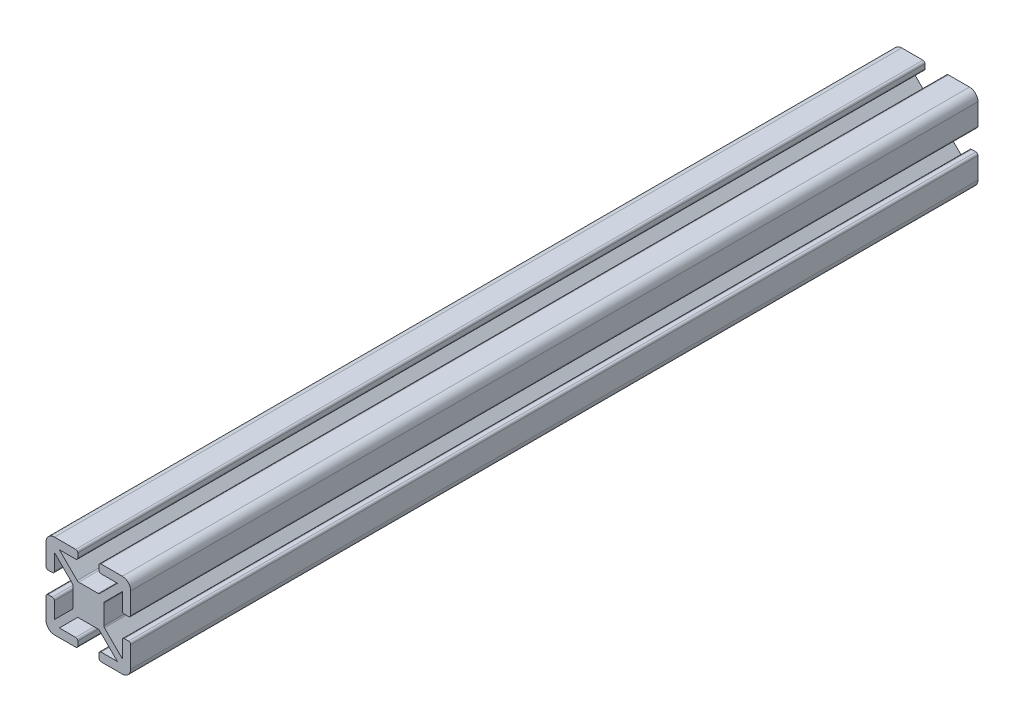
SolidWorks part; units mm, degrees
ref_plane "Ebene vorne" through (0, 0, 0) normal (0, 0, 1) x (1, 0, 0)
ref_plane "Ebene oben" through (0, 0, 0) normal (0, 1, 0) x (1, 0, 0)
ref_plane "Ebene rechts" through (0, 0, 0) normal (1, 0, 0) x (0, 0, -1)
sketch "Skizze1" plane through (0, 0, 0) normal (0, 0, 1) x (1, 0, 0)
  line L0 (-10, 2.5) -> (-8, 2.5)
  line L1 (-10, 10) -> (10, 10) construction
  line L2 (-10, 10) -> (-10, -10) construction
  line L3 (-10, -10) -> (10, -10) construction
  line L4 (10, 10) -> (10, -10) construction
  line L5 (-10, 10) -> (10, -10) construction
  line L6 (-10, -10) -> (10, 10) construction
  line L7 (-8, 2.5) -> (-8, 6.85)
  line L8 (-8, 6.85) -> (-3.65, 2.5)
  line L9 (-10, -2.5) -> (-10, -10)
  line L10 (-10, -10) -> (-2.5, -10)
  line L11 (-3.65, 2.5) -> (-3.65, -2.5)
  line L12 (-3.65, -2.5) -> (-8, -6.85)
  line L13 (-8, -6.85) -> (-8, -2.5)
  line L14 (2.5, -10) -> (10, -10)
  line L15 (10, -10) -> (10, -2.5)
  line L16 (-8, -2.5) -> (-10, -2.5)
  line L17 (-2.5, 10) -> (-2.5, 8)
  line L18 (-2.5, 8) -> (-6.85, 8)
  line L19 (10, 2.5) -> (10, 10)
  line L20 (10, 10) -> (2.5, 10)
  line L21 (-6.85, 8) -> (-2.5, 3.65)
  line L22 (-2.5, 3.65) -> (2.5, 3.65)
  line L23 (2.5, 3.65) -> (6.85, 8)
  line L24 (-2.5, 10) -> (-10, 10)
  line L25 (-10, 10) -> (-10, 2.5)
  line L26 (6.85, 8) -> (2.5, 8)
  line L27 (2.5, 8) -> (2.5, 10)
  line L28 (10, 2.5) -> (8, 2.5)
  line L29 (8, 2.5) -> (8, 6.85)
  line L30 (8, 6.85) -> (3.65, 2.5)
  line L31 (3.65, 2.5) -> (3.65, -2.5)
  line L32 (3.65, -2.5) -> (8, -6.85)
  line L33 (8, -6.85) -> (8, -2.5)
  line L34 (8, -2.5) -> (10, -2.5)
  line L35 (-2.5, -10) -> (-2.5, -8)
  line L36 (-2.5, -8) -> (-6.85, -8)
  line L37 (-6.85, -8) -> (-2.5, -3.65)
  line L38 (-2.5, -3.65) -> (2.5, -3.65)
  line L39 (2.5, -3.65) -> (6.85, -8)
  line L40 (6.85, -8) -> (2.5, -8)
  line L41 (2.5, -8) -> (2.5, -10)
  point P0 (0, 0)
  point P7 (-3.65, 0)
  point P43 (3.65, 0)
  point P44 (0, 3.65)
  point P45 (0, -3.65)
  point P46 (0, 0)
  point P47 (-1.65, 5.3653)
  point P48 (-6, 8)
  point P49 (0, 0)
  point P50 (0, 0)
  point P51 (0, 0)
  point P52 (0, 0)
  point P53 (0, 0)
  point P54 (0, 0)
  point P55 (0, 0)
  point P56 (0, 0)
  dimension "D1" = 20
  dimension "D2" = 6.35
  dimension "D3" = 2
  dimension "D4" = 5
  dimension "D5" = 45
  dimension "D6" = 45
extrude "Aufsatz-Linear austragen1" add sketch "Skizze1" along normal blind 200 contours L24 L25 L0 L7 L8 L11 L12 L13 L16 L9 L10 L35 L36 L37 L38 L39 L40 L41 L14 L15 L34 L33 L32 L31 L30 L29 L28 L19 L20 L27 L26 L23 L22 L21 L18 L17
fillet "Verrundung1" radius 2 4 edges at (-10, -10, 100) (10, -10, 100) (10, 10, 100) (-10, 10, 100)
fillet "Verrundung2" radius 0.5 24 edges at (2.5, -3.65, 100) (-2.5, -3.65, 100) (-3.65, -2.5, 100) (-3.65, 2.5, 100) (2.5, 3.65, 100) (-2.5, 3.65, 100) (2.5, 8, 100) (-2.5, 8, 100) (2.5, 10, 100) (-2.5, 10, 100) (-8, 2.5, 100) (-8, -2.5, 100) (-2.5, -8, 100) (2.5, -8, 100) (8, -2.5, 100) (3.65, -2.5, 100) (3.65, 2.5, 100) (8, 2.5, 100) (10, 2.5, 100) (10, -2.5, 100) (2.5, -10, 100) (-2.5, -10, 100) (-10, -2.5, 100) (-10, 2.5, 100)
